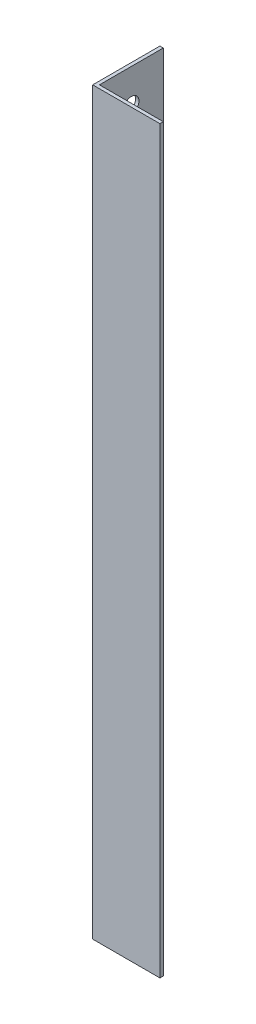
SolidWorks part; units mm, degrees
material "1060 Сплав"
ref_plane "Спереди" through (0, 0, 0) normal (0, 0, 1) x (1, 0, 0)
ref_plane "Сверху" through (0, 0, 0) normal (0, 1, 0) x (1, 0, 0)
ref_plane "Справа" through (0, 0, 0) normal (1, 0, 0) x (0, 0, -1)
sketch "Эскиз1" plane through (0, 0, 0) normal (0, 1, 0) x (1, 0, 0)
  line L0 (0, 0) -> (0, 20)
  line L1 (0, 20) -> (1, 20)
  line L2 (1, 20) -> (1, 1)
  line L3 (1, 1) -> (20, 1)
  line L4 (20, 1) -> (20, 0)
  line L5 (20, 0) -> (0, 0)
  dimension "D1" = 1
  dimension "D2" = 20
extrude "Бобышка-Вытянуть1" add sketch "Эскиз1" along normal blind 220
sketch "Эскиз2" plane through (1, 0, 0) normal (1, 0, 0) x (0, 0, -1)
  line L0 (10.5, 220) -> (10.5, 0) construction
  line L1 (1, 220) -> (20, 220) construction
  line L2 (1, 0) -> (20, 0) construction
  circle A0 centre (10.5, 180) radius 4.25
  circle A1 centre (10.5, 120) radius 4.25
  circle A2 centre (10.5, 60) radius 4.25
  dimension "D1" = 40
  dimension "D2" = 8.5
  dimension "D4" = 60
  dimension "D5" = 60
  dimension "D3" = 3
extrude "Вырез-Вытянуть1" cut sketch "Эскиз2" against normal through all
sketch "Эскиз3" plane through (1, 0, 0) normal (1, 0, 0) x (0, 0, -1)
  circle A0 centre (10.5, 210) radius 2.25 construction
  circle A1 centre (10.5, 210) radius 2.25
extrude "Вырез-Вытянуть2" cut sketch "Эскиз3" against normal through all
sketch "Эскиз4" plane through (1, 0, 0) normal (1, 0, 0) x (0, 0, -1)
  circle A0 centre (10.5, 10) radius 2.25 construction
  circle A1 centre (10.5, 10) radius 2.25
extrude "Вырез-Вытянуть3" cut sketch "Эскиз4" against normal through all
